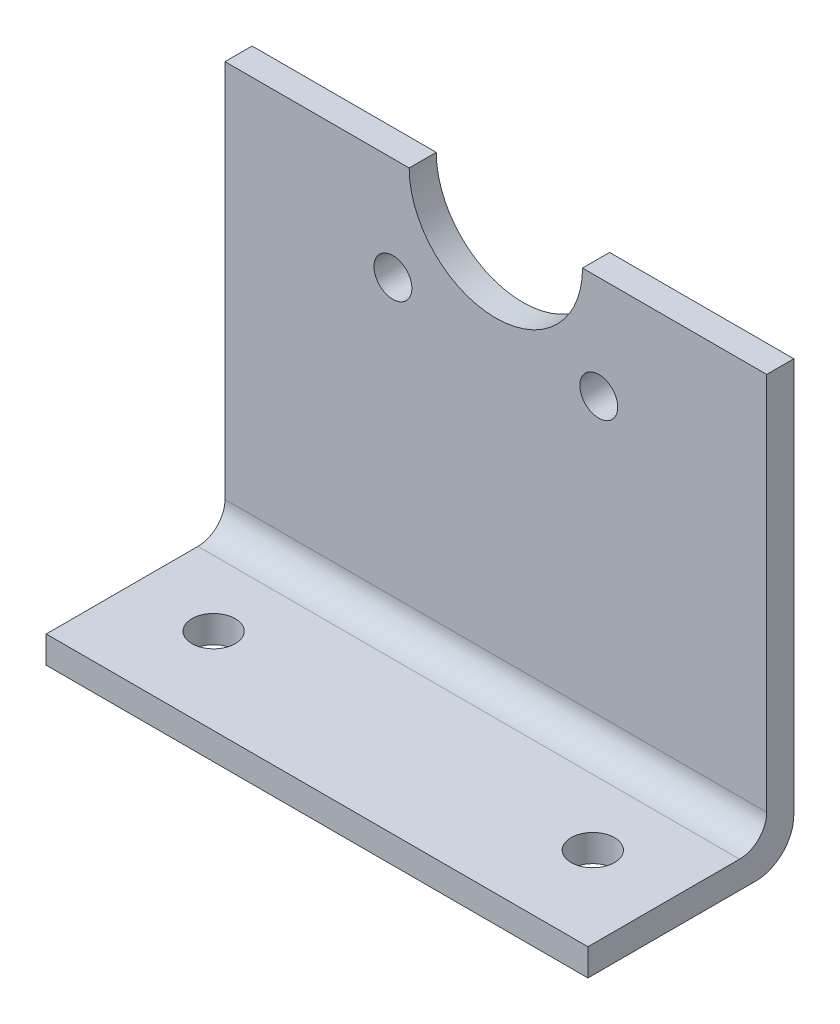
SolidWorks part; units mm, degrees
material "Acciaio al carbonio semplice"
ref_plane "Piano frontale" through (0, 0, 0) normal (0, 0, 1) x (1, 0, 0)
ref_plane "Piano superiore" through (0, 0, 0) normal (0, 1, 0) x (1, 0, 0)
ref_plane "Piano destro" through (0, 0, 0) normal (1, 0, 0) x (0, 0, -1)
sketch "Schizzo1" plane through (0, 0, 0) normal (0, 0, 1) x (1, 0, 0)
  line L0 (66, 80) -> (100, 80)
  line L1 (0, 0) -> (100, 0)
  line L2 (0, 0) -> (0, 80)
  line L3 (0, 80) -> (34, 80)
  line L4 (100, 0) -> (100, 80)
  line L5 (50, 84.7416) -> (50, -4.9988) construction
  arc A0 (34, 80) -> (66, 80) centre (50, 80) ccw
  circle A1 centre (31, 61) radius 3.5
  circle A2 centre (69, 61) radius 3.5
  dimension "D3" = 16
  dimension "D6" = 7
  dimension "D1" = 80
  dimension "D2" = 100
  dimension "D4" = 38
  dimension "D5" = 19
extrude "Estrusione-Estrusione1" add sketch "Schizzo1" along normal blind 5
sketch "Schizzo3" plane through (0, 0, 0) normal (0, 1, 0) x (1, 0, 0)
  line L0 (50, 29.8407) -> (50, -83.9819) construction
  line L1 (100, 0) -> (0, 0)
  line L2 (100, 0) -> (100, -38)
  line L3 (100, -38) -> (0, -38)
  line L4 (0, 0) -> (0, -38)
  line L5 (0, -5) -> (0, 0) construction
  circle A0 centre (15, -22.1) radius 4
  circle A1 centre (85, -22.1) radius 4
  dimension "D4" = 8
  dimension "D1" = 70
  dimension "D2" = 38
  dimension "D3" = 15.9
extrude "Estrusione-Estrusione2" add sketch "Schizzo3" along normal blind 5
fillet "Raccordo1" radius 5 1 edges at (50, 5, 5)
fillet "Raccordo2" radius 7 1 edges at (50, 0, 0)
